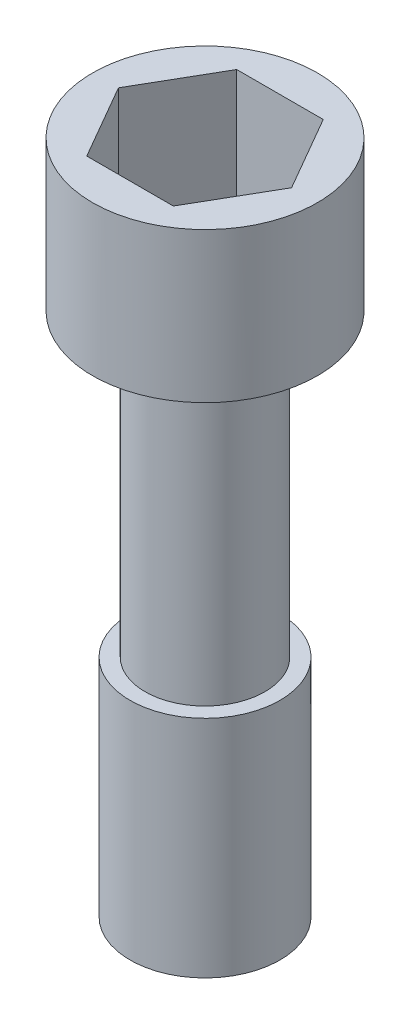
SolidWorks part; units mm, degrees
ref_plane "Front Plane" through (0, 0, 0) normal (0, 0, 1) x (1, 0, 0)
ref_plane "Top Plane" through (0, 0, 0) normal (0, 1, 0) x (1, 0, 0)
ref_plane "Right Plane" through (0, 0, 0) normal (1, 0, 0) x (0, 0, -1)
sketch "Sketch1" plane through (0, 0, 0) normal (0, 1, 0) x (1, 0, 0)
  line L1 (5.7735, 0) -> (2.8868, 5)
  line L2 (2.8868, 5) -> (-2.8868, 5)
  line L3 (-2.8868, 5) -> (-5.7735, 0)
  line L4 (-5.7735, 0) -> (-2.8868, -5)
  line L5 (-2.8868, -5) -> (2.8868, -5)
  line L6 (2.8868, -5) -> (5.7735, 0)
  circle A0 centre (0, 0) radius 7.5
  circle A1 centre (0, 0) radius 5 construction
  point P3 (0, 0)
  dimension "D1" = 10
  dimension "D2" = 15
extrude "Boss-Extrude1" add sketch "Sketch1" along normal blind 8
sketch "Sketch2" plane through (0, 0, 0) normal (0, -1, 0) x (1, 0, 0)
  circle A1 centre (0, 0) radius 7.5
  circle A2 centre (0, 0) radius 7.5
  dimension "D1" = 0
extrude "Boss-Extrude2" add sketch "Sketch2" along normal blind 2
sketch "Sketch3" plane through (0, -2, 0) normal (0, -1, 0) x (1, 0, 0)
  circle A2 centre (0, 0) radius 4
  circle A3 centre (0, 0) radius 4
  dimension "D1" = 3.5
extrude "Boss-Extrude3" add sketch "Sketch3" along normal blind 20
sketch "Sketch4" plane through (0, -22, 0) normal (0, -1, 0) x (1, 0, 0)
  circle A2 centre (0, 0) radius 5
  circle A3 centre (0, 0) radius 5
  dimension "D1" = 1
extrude "Boss-Extrude4" add sketch "Sketch4" along normal blind 15
